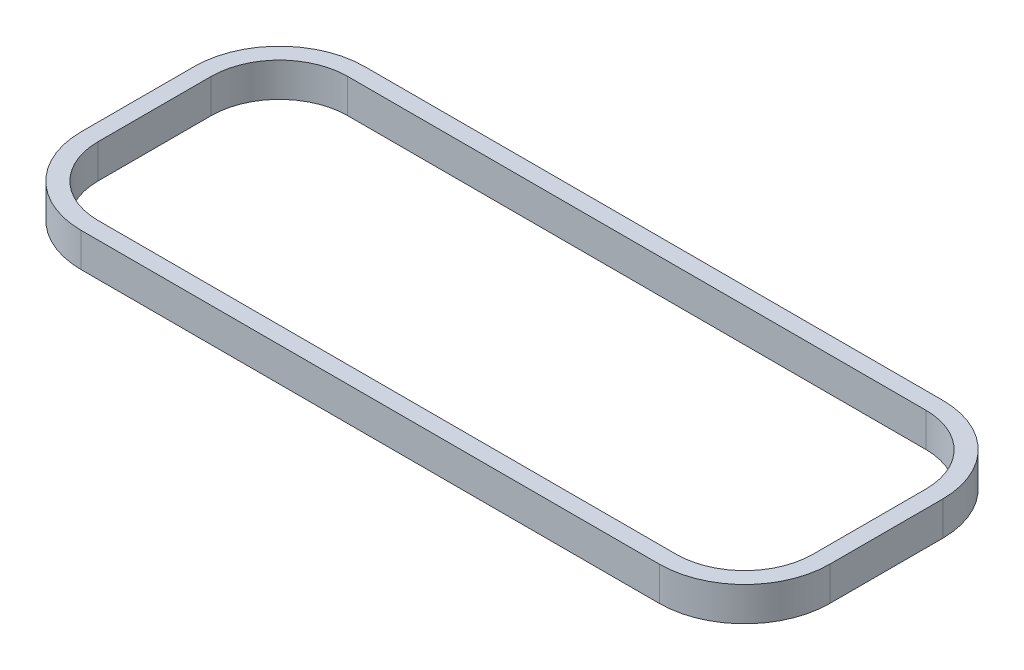
SolidWorks part; units mm, degrees
material "ABS"
ref_plane "Front Plane" through (0, 0, 0) normal (0, 0, 1) x (1, 0, 0)
ref_plane "Top Plane" through (0, 0, 0) normal (0, 1, 0) x (1, 0, 0)
ref_plane "Right Plane" through (0, 0, 0) normal (1, 0, 0) x (0, 0, -1)
sketch "Sketch1" plane through (0, 0, 0) normal (0, 1, 0) x (1, 0, 0)
  line L0 (-161.4161, 5.1814) -> (-161.4161, -58.0646)
  line L1 (-113.6641, -105.8166) -> (209.9319, -105.8166)
  line L2 (257.6839, -58.0646) -> (257.6839, 5.1814)
  line L3 (209.9319, 52.9334) -> (-113.6641, 52.9334)
  line L4 (-151.8911, 5.1814) -> (-151.8911, -58.0646)
  line L5 (-113.6641, -96.2916) -> (209.9319, -96.2916)
  line L6 (248.1589, -58.0646) -> (248.1589, 5.1814)
  line L7 (209.9319, 43.4084) -> (-113.6641, 43.4084)
  arc A0 (-161.4161, -58.0646) -> (-113.6641, -105.8166) centre (-113.6641, -58.0646) ccw
  arc A1 (209.9319, -105.8166) -> (257.6839, -58.0646) centre (209.9319, -58.0646) ccw
  arc A2 (257.6839, 5.1814) -> (209.9319, 52.9334) centre (209.9319, 5.1814) ccw
  arc A3 (-161.4161, 5.1814) -> (-113.6641, 52.9334) centre (-113.6641, 5.1814) cw
  arc A4 (-151.8911, -58.0646) -> (-113.6641, -96.2916) centre (-113.6641, -58.0646) ccw
  arc A5 (209.9319, -96.2916) -> (248.1589, -58.0646) centre (209.9319, -58.0646) ccw
  arc A6 (248.1589, 5.1814) -> (209.9319, 43.4084) centre (209.9319, 5.1814) ccw
  arc A7 (-113.6641, 43.4084) -> (-151.8911, 5.1814) centre (-113.6641, 5.1814) ccw
  dimension "D1" = 47.752
  dimension "D2" = 38.227
  dimension "D3" = 248.1589
  dimension "D4" = 151.8911
  dimension "D5" = 43.4084
  dimension "D6" = 96.2916
extrude "Boss-Extrude1" add sketch "Sketch1" along normal blind 19.05
